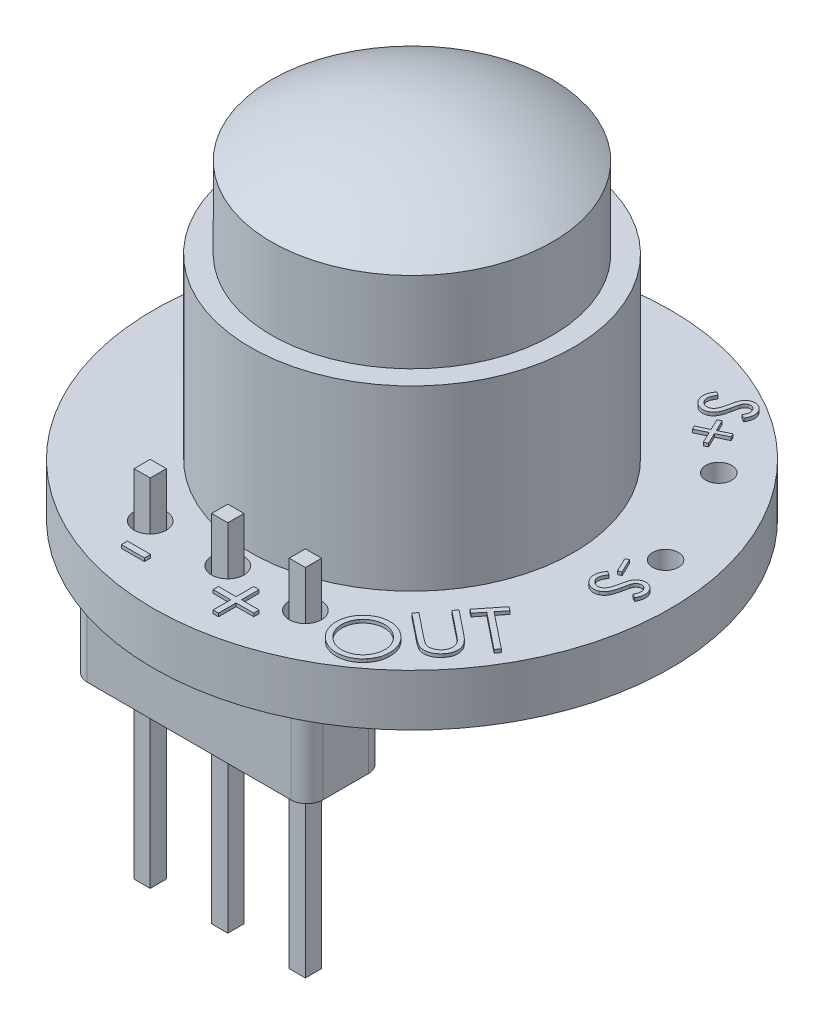
SolidWorks part; units mm, degrees
ref_plane "Front Plane" through (0, 0, 0) normal (0, 0, 1) x (1, 0, 0)
ref_plane "Top Plane" through (0, 0, 0) normal (0, 1, 0) x (1, 0, 0)
ref_plane "Right Plane" through (0, 0, 0) normal (1, 0, 0) x (0, 0, -1)
sketch "Sketch1" plane through (0, 0, 0) normal (0, 0, 1) x (1, 0, 0)
  line L0 (0, 0) -> (0, 13.0973) construction
  line L1 (0, 0) -> (-8, 0) construction
  line L2 (0, 0) -> (-8, 0)
  line L3 (-8, 0) -> (-8, 1.6)
  line L4 (-8, 1.6) -> (-5, 1.6)
  line L5 (-5, 1.6) -> (-5, 7.1)
  line L6 (-5, 7.1) -> (-4.35, 7.1)
  line L7 (-4.35, 7.1) -> (-4.35, 9.6)
  line L8 (-4.35, 9.6) -> (0, 9.6) construction
  line L9 (0, 9.6) -> (4.35, 9.6) construction
  line L10 (0, 0) -> (0, 10.886)
  arc A0 (-4.35, 9.6) -> (0, 10.886) centre (0, 2.886) cw
  dimension "D8" = 8
  dimension "D9" = 1.286
  dimension "D1" = 8
  dimension "D2" = 5
  dimension "D3" = 1.6
  dimension "D4" = 5.5
  dimension "D5" = 2.5
  dimension "D6" = 4.35
  dimension "D7" = 4.35
revolve "Revolve1" add sketch "Sketch1" angle 360 about L10
sketch "Sketch2" plane through (0, 1.6, 0) normal (0, 1, 0) x (1, 0, 0)
  line L0 (-5.6134, -5.7) -> (5.6134, -5.7) construction
  line L1 (0, 0) -> (0, -5.7) construction
  line L2 (3.8502, 7.0125) -> (7.8763, -1.4012) construction
  line L3 (5.8633, 2.8057) -> (9.1443, 4.3757) construction
  circle A0 centre (0, 0) radius 8 construction
  circle A1 centre (0, 0) radius 5 construction
  circle A2 centre (0, -5.7) radius 0.5
  circle A3 centre (-2.4, -5.7) radius 0.5
  circle A4 centre (2.4, -5.7) radius 0.5
  circle A5 centre (5.1079, 4.3843) radius 0.4
  circle A6 centre (6.6187, 1.2271) radius 0.4
  dimension "D2" = 1
  dimension "D3" = 1
  dimension "D4" = 2.4
  dimension "D6" = 0.8
  dimension "D7" = 0.8
  dimension "D8" = 3.5
  dimension "D9" = 1.75
  dimension "D1" = 5.7
  dimension "D5" = 6.5
extrude "Cut-Extrude1" cut sketch "Sketch2" against normal blind 10
ref_plane "Plane1" through (0, -8, 0) normal (0, -1, 0) x (-1, 0, 0)
sketch "Sketch3" plane through (0, -8, 0) normal (0, -1, 0) x (-1, 0, 0)
  line L0 (0, 0) -> (0, -7.3395) construction
  line L1 (0.25, -5.45) -> (-0.25, -5.45)
  line L2 (0.25, -5.45) -> (0.25, -5.95)
  line L3 (0.25, -5.95) -> (-0.25, -5.95)
  line L4 (-0.25, -5.45) -> (-0.25, -5.95)
  line L5 (0.25, -5.45) -> (-0.25, -5.95) construction
  line L6 (0.25, -5.95) -> (-0.25, -5.45) construction
  line L8 (2.65, -5.45) -> (2.15, -5.45)
  line L9 (2.65, -5.45) -> (2.65, -5.95)
  line L10 (2.65, -5.95) -> (2.15, -5.95)
  line L11 (2.15, -5.45) -> (2.15, -5.95)
  line L12 (2.65, -5.45) -> (2.15, -5.95) construction
  line L13 (2.65, -5.95) -> (2.15, -5.45) construction
  line L14 (-2.15, -5.45) -> (-2.65, -5.45)
  line L15 (-2.15, -5.45) -> (-2.15, -5.95)
  line L16 (-2.15, -5.95) -> (-2.65, -5.95)
  line L17 (-2.65, -5.45) -> (-2.65, -5.95)
  line L18 (-2.15, -5.45) -> (-2.65, -5.95) construction
  line L19 (-2.15, -5.95) -> (-2.65, -5.45) construction
  point P0 (2.4, -5.7)
  point P1 (0, -5.7)
  point P3 (-2.4, -5.7)
  point P5 (0, -5.7)
  point P14 (2.4, -5.7)
  point P19 (-2.4, -5.7)
  dimension "D1" = 0.5
  dimension "D2" = 0.5
  dimension "D3" = 0.5
  dimension "D4" = 0.5
  dimension "D5" = 0.5
  dimension "D6" = 0.5
extrude "Boss-Extrude1" add sketch "Sketch3" against normal blind 11 separate body
sketch "Sketch4" plane through (0, 0, 0) normal (0, -1, 0) x (1, 0, 0)
  line L0 (-2.1, 5.99) -> (-2.1, 5.41)
  line L1 (2.7, 5.41) -> (2.1, 5.41)
  line L2 (2.7, 5.41) -> (2.7, 5.99)
  line L3 (2.7, 5.99) -> (2.1, 5.99)
  line L4 (-2.7, 5.41) -> (-2.7, 5.99)
  line L5 (2.7, 5.41) -> (-2.7, 5.99) construction
  line L6 (2.7, 5.99) -> (-2.7, 5.41) construction
  line L7 (3.65, 4.5) -> (-3.65, 4.5)
  line L8 (3.65, 4.5) -> (3.65, 6.9)
  line L9 (3.65, 6.9) -> (-3.65, 6.9)
  line L10 (-3.65, 4.5) -> (-3.65, 6.9)
  line L11 (3.65, 4.5) -> (-3.65, 6.9) construction
  line L12 (3.65, 6.9) -> (-3.65, 4.5) construction
  line L13 (-0.3, 5.99) -> (-0.3, 5.41)
  line L14 (0.3, 5.99) -> (0.3, 5.41)
  line L15 (2.1, 5.99) -> (2.1, 5.41)
  line L16 (-2.1, 5.99) -> (-2.7, 5.99)
  line L17 (-2.1, 5.41) -> (-2.7, 5.41)
  line L18 (0.3, 5.41) -> (-0.3, 5.41)
  line L19 (0.3, 5.99) -> (-0.3, 5.99)
  line L21 (2.15, 5.95) -> (2.15, 5.45) construction
  line L22 (0.25, 5.45) -> (0.25, 5.95) construction
  line L23 (-0.25, 5.95) -> (-0.25, 5.45) construction
  line L24 (-2.15, 5.45) -> (-2.15, 5.95) construction
  point P0 (0, 5.7)
  point P6 (0, 5.7)
  dimension "D1" = 7.3
  dimension "D2" = 2.4
  dimension "D3" = 5.4
  dimension "D4" = 0.58
  dimension "D5" = 0.05
  dimension "D6" = 0.05
  dimension "D7" = 0.05
  dimension "D8" = 0.05
extrude "Boss-Extrude2" add sketch "Sketch4" along normal blind 2.5
fillet "Fillet1" radius 0.5 4 edges at (-3.65, -1.25, 6.9) (3.65, -1.25, 6.9) (-3.65, -1.25, 4.5) (3.65, -1.25, 4.5)
sketch "Sketch5" plane through (0, 1.6, 0) normal (0, 1, 0) x (1, 0, 0)
  line L0 (-2.7839, -7.5) -> (2.7839, -7.5) construction
  circle A0 centre (0, 0) radius 8 construction
  text T0 " -   +" font "Century Gothic" height in points 7
  dimension "D1" = 7.5
extrude "Boss-Extrude3" add sketch "Sketch5" along normal blind 0.1
sketch "Sketch6" plane through (0, 1.6, 0) normal (0, 1, 0) x (1, 0, 0)
  line L0 (4.1279, -6.8528) -> (7.5994, -2.4997) construction
  circle A0 centre (0, 0) radius 8 construction
  circle A1 centre (0, 0) radius 5 construction
  text T0 "OUT" font "Century Gothic" height in points 6
  dimension "D1" = 7.5
extrude "Boss-Extrude4" add sketch "Sketch6" along normal blind 0.1
sketch "Sketch7" plane through (0, 1.6, 0) normal (0, 1, 0) x (1, 0, 0)
  line L0 (-2.8915, 7.4592) -> (-7.8556, 1.513) construction
  circle A0 centre (0, 0) radius 8 construction
  circle A1 centre (0, 0) radius 5 construction
  text T0 "SR602" font "Century Gothic" height in points 6
  dimension "D1" = 7
extrude "Boss-Extrude5" add sketch "Sketch7" along normal blind 0.1
sketch "Sketch8" plane through (0, 1.6, 0) normal (0, 1, 0) x (1, 0, 0)
  line L0 (2.119, 7.7142) -> (7.3459, -3.1683) construction
  circle A0 centre (0, 0) radius 8 construction
  text T0 "   S+         -S" font "Century Gothic" height in points 5
  dimension "D1" = 5.25
extrude "Boss-Extrude6" add sketch "Sketch8" along normal blind 0.1
